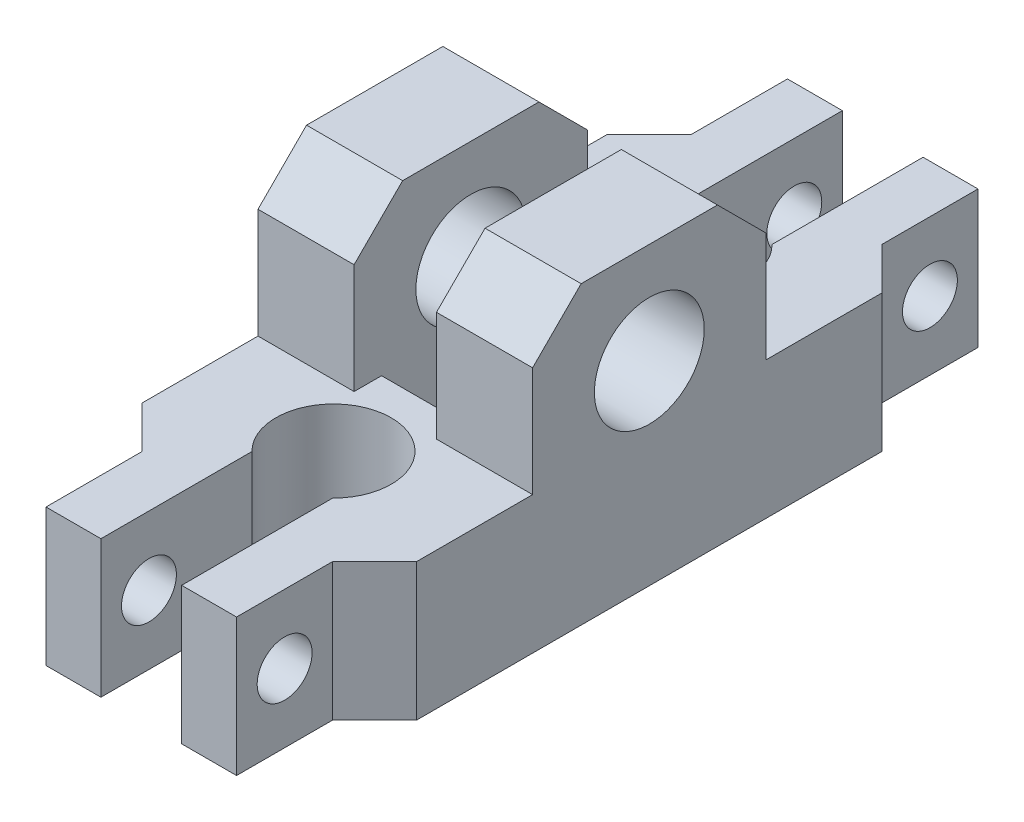
SolidWorks part; units mm, degrees
ref_plane "Front Plane" through (0, 0, 0) normal (0, 0, 1) x (1, 0, 0)
ref_plane "Top Plane" through (0, 0, 0) normal (0, 1, 0) x (1, 0, 0)
ref_plane "Right Plane" through (0, 0, 0) normal (1, 0, 0) x (0, 0, -1)
sketch "Sketch1" plane through (0, 0, 0) normal (0, 1, 0) x (1, 0, 0)
  line L0 (10, 40) -> (10, 33) construction
  line L1 (0, 0) -> (20, 0)
  line L2 (0, 0) -> (0, 40)
  line L3 (0, 40) -> (20, 40)
  line L4 (20, 0) -> (20, 40)
  line L5 (10, 0) -> (10, 7) construction
  line L6 (0, 20) -> (20, 20) construction
  line L7 (12.9394, 0) -> (7.0606, 0)
  line L8 (12.9394, 0) -> (12.9394, 4)
  line L9 (12.9394, 4) -> (7.0606, 4)
  line L10 (7.0606, 0) -> (7.0606, 4)
  line L11 (7.0606, 0) -> (3.0606, 0)
  line L12 (7.0606, 0) -> (7.0606, -7)
  line L13 (7.0606, -7) -> (3.0606, -7)
  line L14 (3.0606, 0) -> (3.0606, -7)
  line L15 (12.9394, 0) -> (16.9394, 0)
  line L16 (12.9394, 0) -> (12.9394, -7)
  line L17 (12.9394, -7) -> (16.9394, -7)
  line L18 (16.9394, 0) -> (16.9394, -7)
  line L19 (7.0606, 47) -> (3.0606, 47)
  line L20 (3.0606, 40) -> (3.0606, 47)
  line L21 (7.0606, 40) -> (3.0606, 40)
  line L22 (7.0606, 40) -> (7.0606, 47)
  line L23 (12.9394, 47) -> (16.9394, 47)
  line L24 (16.9394, 40) -> (16.9394, 47)
  line L25 (12.9394, 40) -> (16.9394, 40)
  line L26 (12.9394, 40) -> (12.9394, 47)
  line L27 (12.9394, 36) -> (7.0606, 36)
  line L28 (7.0606, 40) -> (7.0606, 36)
  line L29 (12.9394, 40) -> (7.0606, 40)
  line L30 (12.9394, 40) -> (12.9394, 36)
  circle A0 centre (10, 33) radius 4.2
  circle A1 centre (10, 7) radius 4.2
  point P11 (10, 4)
  dimension "D1" = 8.4
  dimension "D2" = 26
  dimension "D3" = 40
  dimension "D4" = 20
  dimension "D5" = 4
  dimension "D6" = 4
  dimension "D7" = 7
extrude "Boss-Extrude1" add sketch "Sketch1" along normal blind 10 contours A1 L8 L1 L4 L3 L30 A0 L28 L2 L10 | L18 L1 L16 L17 | L1 L14 L13 L12 | L26 L3 L24 L23 | L3 L22 L19 L20
sketch "Sketch2" plane through (20, 0, 0) normal (1, 0, 0) x (0, 0, -1)
  line L1 (28.5, 0) -> (11.5, 0)
  line L3 (24.9645, 21.5355) -> (15.0355, 21.5355)
  line L5 (20, 21.5355) -> (20, 0) construction
  line L6 (15.0355, 21.5355) -> (11.5, 21.5355) construction
  line L8 (11.5, 21.5355) -> (11.5, 18) construction
  line L9 (11.5, 18) -> (15.0355, 21.5355)
  line L10 (24.9645, 21.5355) -> (28.5, 18)
  line L11 (28.5, 18) -> (28.5, 0)
  line L12 (11.5, 18) -> (11.5, 0)
  line L13 (24.9645, 21.5355) -> (28.5, 21.5355) construction
  line L14 (28.5, 21.5355) -> (28.5, 18) construction
  line L15 (0, 0) -> (40, 0) construction
  circle A0 centre (20, 14.1905) radius 4
  point P8 (20, 0)
  dimension "D3" = 8
  dimension "D1" = 17
  dimension "D2" = 18
  dimension "D4" = 5
  dimension "D5" = 7.345
extrude "Boss-Extrude2" add sketch "Sketch2" against normal up to surface (20 mm away) up to face at (0, 5, -20)
sketch "Sketch3" plane through (0, 21.5355, 0) normal (0, 1, 0) x (1, 0, 0)
  line L1 (7, 26.5) -> (13, 26.5)
  line L2 (7, 26.5) -> (7, 13.5)
  line L3 (7, 13.5) -> (13, 13.5)
  line L4 (13, 26.5) -> (13, 13.5)
  line L8 (10, 26.5) -> (10, 13.5) construction
  line L9 (0, 15.0355) -> (20, 15.0355) construction
  line L10 (7, 11.5) -> (13, 11.5) construction
  line L11 (7, 28.5) -> (13, 28.5) construction
  line L12 (0, 11.5) -> (20, 11.5) construction
  line L13 (0, 28.5) -> (20, 28.5) construction
  point P12 (10, 15.0355)
  dimension "D1" = 6
  dimension "D2" = 2
  dimension "D3" = 2
extrude "Cut-Extrude1" cut sketch "Sketch3" against normal blind 16
sketch "Sketch4" plane through (0, 0, -11.5) normal (0, 0, 1) x (1, 0, 0)
  line L0 (0, 10) -> (20, 10) construction
  line L1 (7, 10) -> (13, 10)
  line L2 (7, 10) -> (7, 20)
  line L3 (7, 20) -> (13, 20)
  line L4 (13, 10) -> (13, 20)
  line L5 (7, 20) -> (13, 20) construction
  point P6 (10, 10)
  point P9 (10, 10)
  dimension "D1" = 6
extrude "Cut-Extrude2" cut sketch "Sketch4" against normal through all
sketch "Sketch5" plane through (3.0606, 0, 0) normal (-1, 0, 0) x (0, 0, 1)
  line L0 (-20, -0.0187) -> (-20, 30.8761) construction
  line L1 (-47, 0) -> (7, 0) construction
  line L2 (-43.5, 10) -> (-43.5, 0) construction
  line L3 (-40, 10) -> (-47, 10) construction
  line L4 (3.5, 10) -> (3.5, 0) construction
  line L5 (0, 10) -> (7, 10) construction
  circle A0 centre (3.5, 5) radius 2
  circle A1 centre (-43.5, 5) radius 2
  point P10 (-20, 0)
  dimension "D1" = 4
extrude "Cut-Extrude3" cut sketch "Sketch5" against normal through all
sketch "Sketch6" plane through (0, 10, 0) normal (0, 1, 0) x (1, 0, 0)
  line L0 (16.9394, 40) -> (20, 36.9394)
  line L1 (20, 28.5) -> (20, 40) construction
  line L2 (20, 36.9394) -> (20, 40)
  line L3 (20, 40) -> (16.9394, 40)
  line L4 (10, 28.8) -> (10, 26.5) construction
  line L6 (13, 26.5) -> (7, 26.5) construction
  line L7 (0, 40) -> (3.0606, 40)
  line L8 (0, 36.9394) -> (0, 40)
  line L9 (3.0606, 40) -> (0, 36.9394)
  line L10 (12.9394, -7) -> (12.9394, 47) construction
  line L11 (12.9394, 20) -> (-5.4645, 20) construction
  line L12 (3.0606, 0) -> (0, 3.0606)
  line L13 (0, 3.0606) -> (0, 0)
  line L14 (0, 0) -> (3.0606, 0)
  line L15 (20, 0) -> (16.9394, 0)
  line L16 (20, 3.0606) -> (20, 0)
  line L17 (16.9394, 0) -> (20, 3.0606)
  point P10 (10, 26.5)
  point P20 (12.9394, 20)
extrude "Cut-Extrude4" cut sketch "Sketch6" against normal up to surface (10 mm away) up to face at (10, 0, -20)
equation "\"8mm hole\" = 8.4mm"
equation "\"22mm hole\"= 23mm"
equation "\"15mm hole\"= 15.8mm"
equation "\"bed height offset\"= 3mm"
equation "\"motor width\"= 42.5mm"
equation "\"D1@Sketch1\"= \"8mm hole\""
